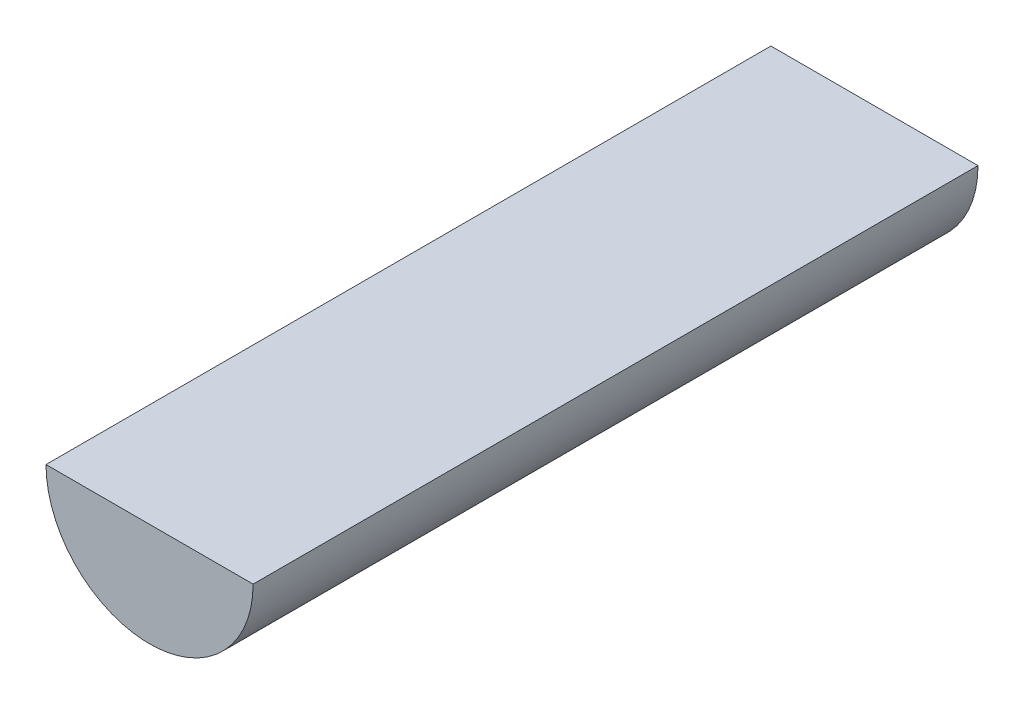
SolidWorks part; units mm, degrees
material "Polyurethane Foam Rigid"
ref_plane "Front Plane" through (0, 0, 0) normal (0, 0, 1) x (1, 0, 0)
ref_plane "Top Plane" through (0, 0, 0) normal (0, 1, 0) x (1, 0, 0)
ref_plane "Right Plane" through (0, 0, 0) normal (1, 0, 0) x (0, 0, -1)
sketch "Sketch1" plane through (0, 0, 0) normal (0, 0, 1) x (1, 0, 0)
  line L0 (-186.944, 0) -> (203.2, 0) construction
  line L1 (0, 176.784) -> (0, -193.04) construction
  line L2 (-101.6, 0) -> (101.6, 0)
  arc A0 (-101.6, 0) -> (101.6, 0) centre (0, 0) ccw
  dimension "D1" = 203.2
extrude "Boss-Extrude1" add sketch "Sketch1" along normal blind 711.2
